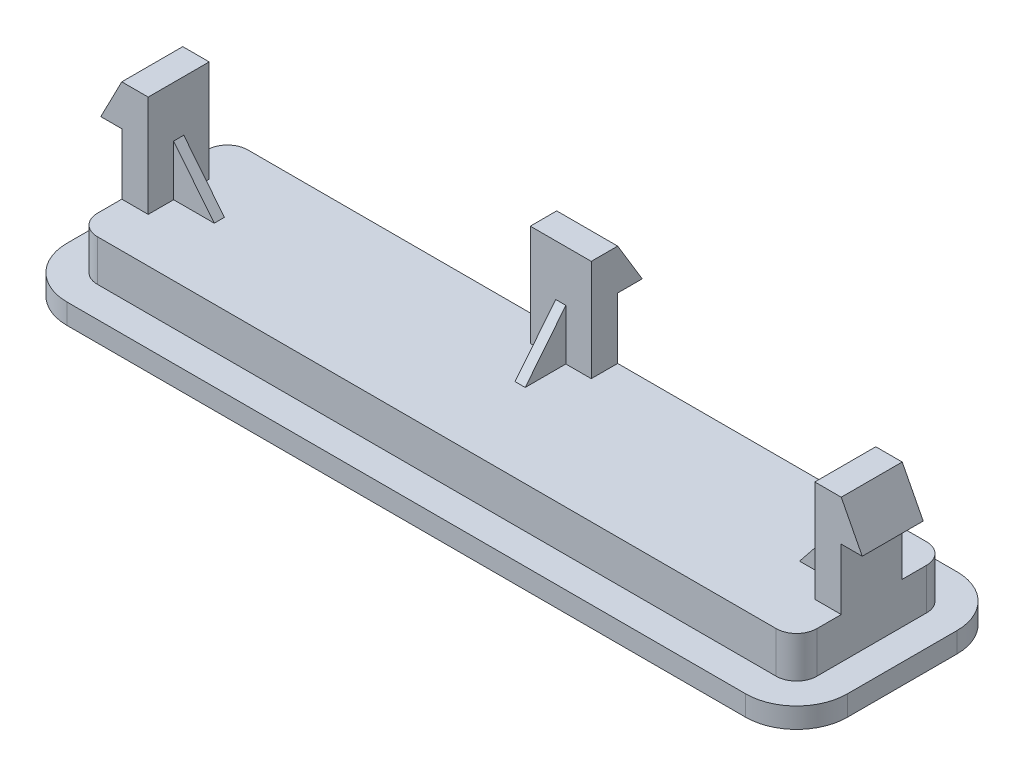
SolidWorks part; units mm, degrees
ref_plane "Front Plane" through (0, 0, 0) normal (0, 0, 1) x (1, 0, 0)
ref_plane "Top Plane" through (0, 0, 0) normal (0, 1, 0) x (1, 0, 0)
ref_plane "Right Plane" through (0, 0, 0) normal (1, 0, 0) x (0, 0, -1)
sketch "Sketch1" plane through (0, 0, 0) normal (0, 1, 0) x (1, 0, 0)
  line L1 (-16.7, -3.7) -> (16.7, -3.7)
  line L2 (-17.7, -2.7) -> (-17.7, 2.7)
  line L3 (-16.7, 3.7) -> (16.7, 3.7)
  line L4 (17.7, -2.7) -> (17.7, 2.7)
  line L5 (-17.7, -3.7) -> (17.7, 3.7) construction
  line L6 (-17.7, 3.7) -> (17.7, -3.7) construction
  arc A0 (16.7, -3.7) -> (17.7, -2.7) centre (16.7, -2.7) ccw
  arc A1 (16.7, 3.7) -> (17.7, 2.7) centre (16.7, 2.7) cw
  arc A2 (-17.7, 2.7) -> (-16.7, 3.7) centre (-16.7, 2.7) cw
  arc A3 (-16.7, -3.7) -> (-17.7, -2.7) centre (-16.7, -2.7) cw
  point P0 (0, 0)
  dimension "D3" = 1
  dimension "D1" = 35.4
  dimension "D2" = 7.4
extrude "Boss-Extrude1" add sketch "Sketch1" along normal blind 3.03
sketch "Sketch2" plane through (0, 0, 0) normal (0, -1, 0) x (1, 0, 0)
  line L8 (16.7, 5.2) -> (-16.7, 5.2)
  line L9 (-19.2, 2.7) -> (-19.2, -2.7)
  line L10 (-16.7, -5.2) -> (16.7, -5.2)
  line L11 (19.2, -2.7) -> (19.2, 2.7)
  line L12 (16.7, 5.2) -> (-16.7, 5.2)
  line L13 (-19.2, 2.7) -> (-19.2, -2.7)
  line L14 (-16.7, -5.2) -> (16.7, -5.2)
  line L15 (19.2, -2.7) -> (19.2, 2.7)
  arc A8 (19.2, 2.7) -> (16.7, 5.2) centre (16.7, 2.7) ccw
  arc A9 (-16.7, 5.2) -> (-19.2, 2.7) centre (-16.7, 2.7) ccw
  arc A10 (-19.2, -2.7) -> (-16.7, -5.2) centre (-16.7, -2.7) ccw
  arc A11 (16.7, -5.2) -> (19.2, -2.7) centre (16.7, -2.7) ccw
  arc A12 (19.2, 2.7) -> (16.7, 5.2) centre (16.7, 2.7) ccw
  arc A13 (-16.7, 5.2) -> (-19.2, 2.7) centre (-16.7, 2.7) ccw
  arc A14 (-19.2, -2.7) -> (-16.7, -5.2) centre (-16.7, -2.7) ccw
  arc A15 (16.7, -5.2) -> (19.2, -2.7) centre (16.7, -2.7) ccw
  dimension "D1" = 1.5
extrude "Boss-Extrude2" add sketch "Sketch2" against normal blind 1
sketch "Sketch3" plane through (0, 3.03, 0) normal (0, 1, 0) x (1, 0, 0)
  line L0 (-17.7, 0) -> (0, 0) construction
  line L1 (-17.7, -2.7) -> (-17.7, 2.7) construction
  line L2 (0, 0) -> (0, 3.7) construction
  line L3 (-17.7, 1.5) -> (-16.4, 1.5)
  line L4 (-17.7, 1.5) -> (-17.7, -1.5)
  line L5 (-17.7, -1.5) -> (-16.4, -1.5)
  line L6 (-16.4, 1.5) -> (-16.4, -1.5)
  line L7 (16.7, 3.7) -> (-16.7, 3.7) construction
  line L9 (0, 3.7) -> (-1.5, 3.7)
  line L10 (0, 3.7) -> (0, 2.4)
  line L11 (0, 2.4) -> (-1.5, 2.4)
  line L12 (-1.5, 3.7) -> (-1.5, 2.4)
  point P9 (-16.4, 0)
  dimension "D1" = 3
  dimension "D2" = 1.3
  dimension "D3" = 1.3
  dimension "D4" = 1.5
extrude "Boss-Extrude3" add sketch "Sketch3" along normal blind 5
sketch "Sketch5" plane through (0, 0, 1.5) normal (0, 0, 1) x (1, 0, 0)
  line L0 (-17.7, 8.03) -> (-18.7333, 6.03)
  line L1 (-17.7, 8.03) -> (-16.4, 8.03) construction
  line L2 (-18.7333, 6.03) -> (-17.7, 6.03)
  line L3 (-17.7, 8.03) -> (-17.7, 3.03) construction
  line L4 (-17.7, 6.03) -> (-17.7, 8.03)
  dimension "D1" = 2
extrude "Boss-Extrude4" add sketch "Sketch5" against normal up to surface (3 mm away) up to face at (-17.05, 5.53, -1.5)
sketch "Sketch8" plane through (-1.5, 0, 0) normal (-1, 0, 0) x (0, 0, 1)
  line L0 (-3.7, 8.03) -> (-4.9103, 6.03)
  line L1 (-3.7, 8.03) -> (-2.4, 8.03) construction
  line L2 (-4.9103, 6.03) -> (-3.7, 6.03)
  line L3 (-3.7, 8.03) -> (-3.7, 3.03) construction
  line L4 (-3.7, 6.03) -> (-3.7, 8.03)
  dimension "D1" = 2
extrude "Boss-Extrude5" add sketch "Sketch8" against normal up to surface (1.5 mm away) up to face at (0, 5.53, -3.05)
sketch "Sketch9" plane through (-16.4, 0, 0) normal (1, 0, 0) x (0, 0, -1)
  line L0 (-1.5, 5.53) -> (1.5, 5.53) construction
  line L1 (-1.5, 8.03) -> (-1.5, 3.03) construction
  line L2 (1.5, 8.03) -> (1.5, 3.03) construction
  line L3 (0, 5.53) -> (0, 3.03) construction
  line L4 (-1.5, 3.03) -> (1.5, 3.03) construction
  line L6 (-0.25, 3.03) -> (0.25, 3.03)
  line L7 (-0.25, 3.03) -> (-0.25, 5.53)
  line L8 (-0.25, 5.53) -> (0.25, 5.53)
  line L9 (0.25, 3.03) -> (0.25, 5.53)
  line L10 (-0.25, 3.03) -> (0.25, 5.53) construction
  line L11 (-0.25, 5.53) -> (0.25, 3.03) construction
  point P10 (0, 4.28)
  dimension "D1" = 0.5
extrude "Boss-Extrude6" add sketch "Sketch9" along normal blind 2
sketch "Sketch10" plane through (0, 0, 0.25) normal (0, 0, 1) x (1, 0, 0)
  line L0 (-16.4, 5.53) -> (-14.4, 3.03)
  line L1 (-14.4, 3.03) -> (-14.4, 5.53)
  line L2 (-14.4, 5.53) -> (-16.4, 5.53)
extrude "Cut-Extrude1" cut sketch "Sketch10" against normal up to next (0.5 mm away)
sketch "Sketch11" plane through (0, 0, -2.4) normal (0, 0, 1) x (1, 0, 0)
  line L0 (0, 8.03) -> (0, 3.03) construction
  line L1 (0, 5.53) -> (-0.25, 5.53)
  line L2 (0, 5.53) -> (0, 3.03)
  line L3 (0, 3.03) -> (-0.25, 3.03)
  line L4 (-0.25, 5.53) -> (-0.25, 3.03)
  line L5 (-1.5, 3.03) -> (0, 3.03) construction
  dimension "D1" = 0.25
extrude "Boss-Extrude7" add sketch "Sketch11" along normal blind 2
sketch "Sketch12" plane through (-0.25, 0, 0) normal (-1, 0, 0) x (0, 0, 1)
  line L0 (-2.4, 5.53) -> (-0.4, 3.03)
  line L1 (-0.4, 3.03) -> (-0.4, 5.53)
  line L2 (-0.4, 5.53) -> (-2.4, 5.53)
extrude "Cut-Extrude2" cut sketch "Sketch12" against normal up to next (0.25 mm away)
mirror "Mirror1" about plane through (0, 0, 0) normal (1, 0, 0) of "Boss-Extrude3", "Boss-Extrude4", "Boss-Extrude5", "Boss-Extrude7", "Cut-Extrude1", "Boss-Extrude6", "Cut-Extrude2"
